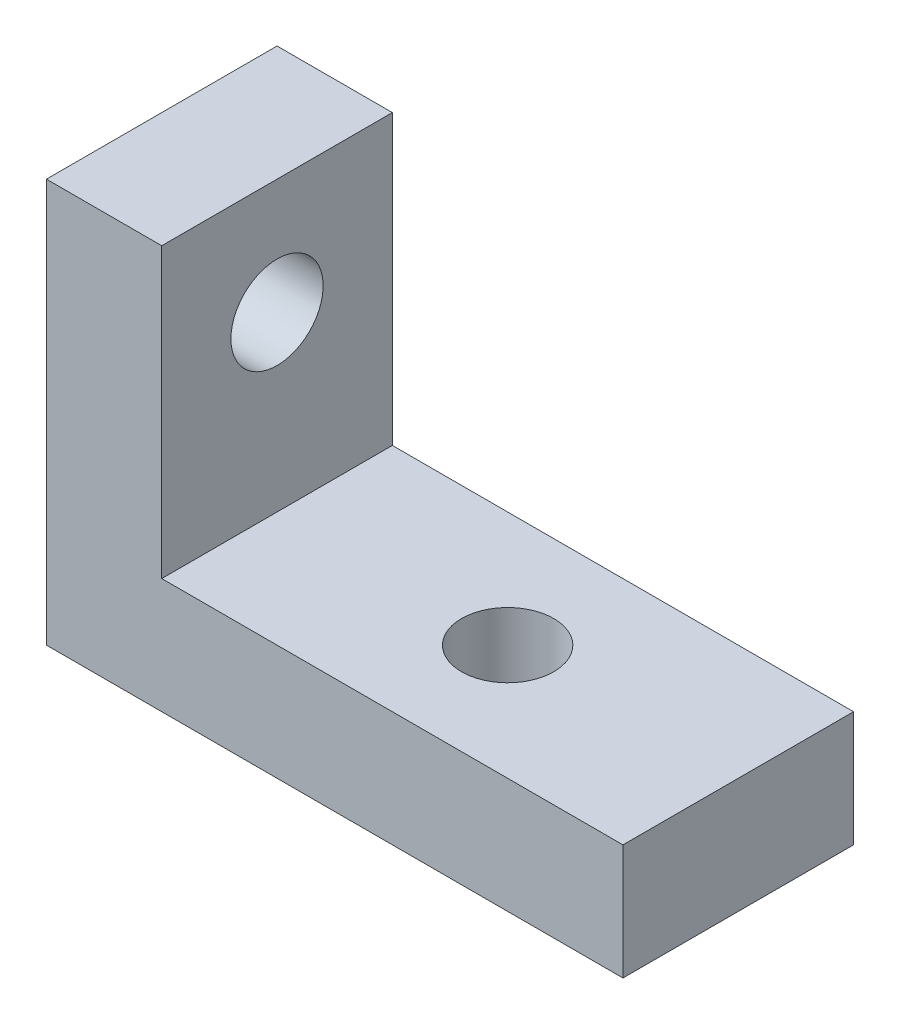
SolidWorks part; units mm, degrees
ref_plane "Front Plane" through (0, 0, 0) normal (0, 0, 1) x (1, 0, 0)
ref_plane "Top Plane" through (0, 0, 0) normal (0, 1, 0) x (1, 0, 0)
ref_plane "Right Plane" through (0, 0, 0) normal (1, 0, 0) x (0, 0, -1)
sketch "Sketch1" plane through (0, 0, 0) normal (0, 0, 1) x (1, 0, 0)
  line L0 (-15.9173, -20.9973) -> (-15.9173, -29.8873)
  line L1 (-3.2173, -29.8873) -> (-3.2173, -27.3473)
  line L2 (-3.2173, -27.3473) -> (-13.3773, -27.3473)
  line L3 (-13.3773, -27.3473) -> (-13.3773, -20.9973)
  line L4 (-13.3773, -20.9973) -> (-15.9173, -20.9973)
  line L5 (-15.9173, -29.8873) -> (-3.2173, -29.8873)
  dimension "D1" = 2.54
  dimension "D2" = 2.54
  dimension "D3" = 8.89
  dimension "D4" = 10.16
extrude "Boss-Extrude2" add sketch "Sketch1" along normal blind 5.08 contours L3 L4 L0 L5 L1 L2
sketch "Sketch3" plane through (0, -27.3473, 0) normal (0, 1, 0) x (1, 0, 0)
  line L0 (-3.2173, -5.08) -> (-3.2173, 0) construction
  line L1 (-3.2173, 0) -> (-13.3773, 0) construction
  circle A0 centre (-8.2973, -2.54) radius 1.016
  dimension "D1" = 5.08
  dimension "D2" = 2.54
extrude "Cut-Extrude1" cut sketch "Sketch3" against normal blind 25.4
sketch "Sketch4" plane through (-15.9173, 0, 0) normal (-1, 0, 0) x (0, 0, 1)
  line L1 (0, -20.9973) -> (0, -29.8873) construction
  line L3 (5.08, -29.8873) -> (0, -29.8873) construction
  circle A0 centre (2.54, -23.5373) radius 1.016
  dimension "D1" = 2.54
  dimension "D2" = 6.35
extrude "Cut-Extrude2" cut sketch "Sketch4" against normal blind 2.54
